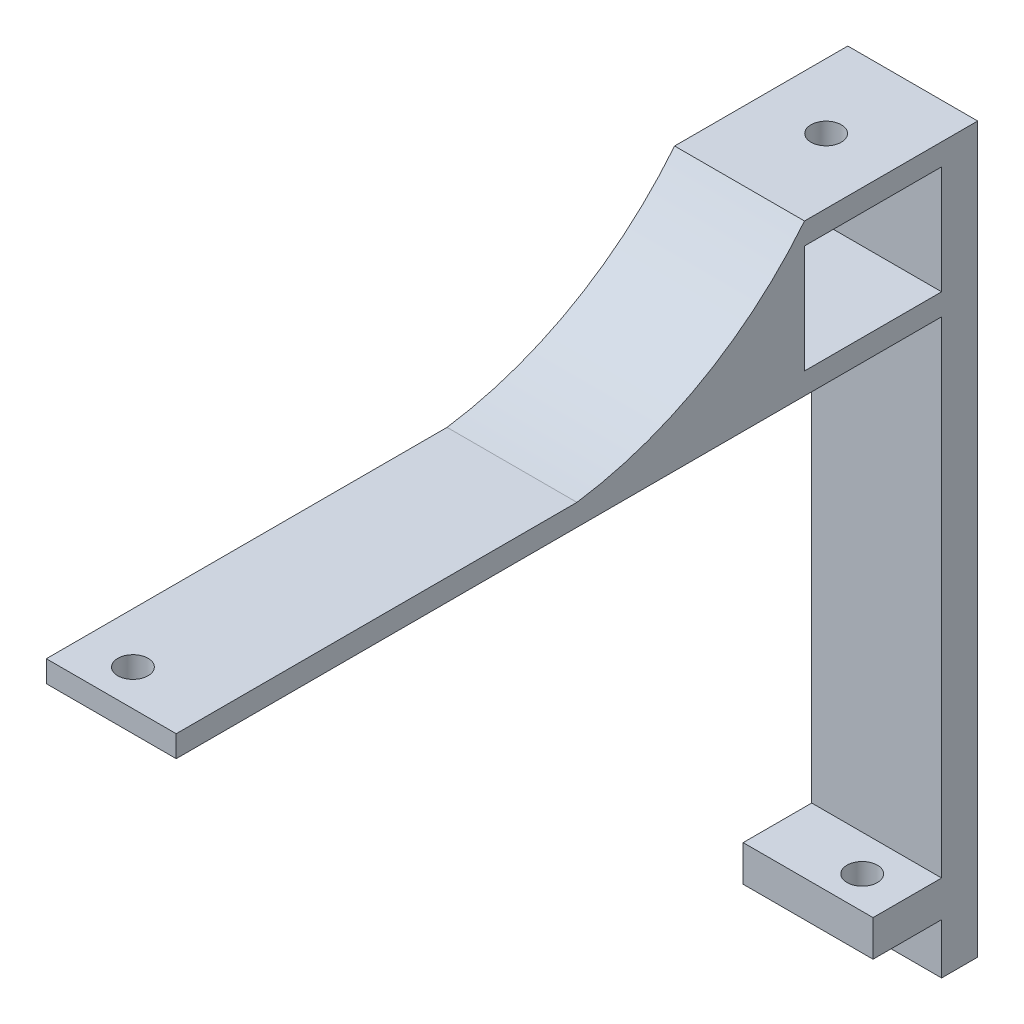
SolidWorks part; units mm, degrees
ref_plane "Front Plane" through (0, 0, 0) normal (0, 0, 1) x (1, 0, 0)
ref_plane "Top Plane" through (0, 0, 0) normal (0, 1, 0) x (1, 0, 0)
ref_plane "Right Plane" through (0, 0, 0) normal (1, 0, 0) x (0, 0, -1)
sketch "Sketch3" plane through (0, 0, 0) normal (1, 0, 0) x (0, 0, -1)
  line L1 (22.6396, 117.064) -> (32.6396, 117.064)
  line L2 (22.6396, 117.064) -> (22.6396, 192.4144)
  line L3 (22.6396, 192.4144) -> (32.6396, 192.4144)
  line L4 (32.6396, 117.064) -> (32.6396, 192.4144)
  line L6 (-73.4248, 192.4144) -> (22.6396, 192.4144)
  line L8 (-73.4248, 189.4144) -> (22.6396, 189.4144)
  line L9 (22.6396, 192.4144) -> (22.6396, 189.4144)
  line L10 (-63.4248, 192.4144) -> (-63.4248, 189.4144)
  line L11 (-73.4248, 192.4144) -> (-73.4248, 189.4144)
  line L12 (37.6396, 117.064) -> (32.6396, 117.064)
  line L13 (32.6396, 192.4144) -> (37.6396, 192.4144)
  line L14 (32.6396, 192.4144) -> (32.6396, 110.064)
  line L15 (32.6396, 110.064) -> (37.6396, 110.064)
  line L16 (37.6396, 192.4144) -> (37.6396, 110.064)
  line L17 (32.6396, 122.064) -> (22.6396, 122.064)
  dimension "D1" = 10
  dimension "D2" = 0
  dimension "D3" = 10
  dimension "D4" = 5
  dimension "D5" = 5
sketch "Sketch4" plane through (0, 0, 0) normal (1, 0, 0) x (0, 0, -1)
  line L1 (22.6396, 122.064) -> (32.6396, 122.064)
  line L2 (22.6396, 122.064) -> (22.6396, 117.064)
  line L3 (22.6396, 117.064) -> (32.6396, 117.064)
  line L4 (32.6396, 122.064) -> (32.6396, 117.064)
  line L5 (37.6396, 110.064) -> (32.6396, 110.064)
  line L6 (37.6396, 110.064) -> (37.6396, 192.4144)
  line L7 (37.6396, 192.4144) -> (32.6396, 192.4144)
  line L8 (32.6396, 110.064) -> (32.6396, 192.4144)
  line L9 (-73.4248, 192.4144) -> (32.6396, 192.4144)
  line L10 (-73.4248, 192.4144) -> (-73.4248, 189.4144)
  line L11 (-73.4248, 189.4144) -> (32.6396, 189.4144)
  line L12 (32.6396, 192.4144) -> (32.6396, 189.4144)
extrude "Boss-Extrude1" add sketch "Sketch4" along normal blind 52 contours L10 L11 L8 L9 | L8 L5 L6 L7 L4 | L4 L1 L2 L3
sketch "Sketch5" plane through (0, 122.064, 0) normal (0, 1, 0) x (1, 0, 0)
  line L0 (26, 22.6396) -> (26, 32.6396) construction
  line L1 (52, 22.6396) -> (0, 22.6396) construction
  line L2 (52, 32.6396) -> (0, 32.6396) construction
  circle A0 centre (6, 27.0496) radius 2.1
  circle A1 centre (46, 27.6396) radius 2.1
  dimension "D1" = 4.2
  dimension "D2" = 4.2
  dimension "D3" = 20
  dimension "D4" = 20
  dimension "D5" = 4.41
  dimension "D6" = 5
extrude "Cut-Extrude1" cut sketch "Sketch5" against normal blind 52
sketch "Sketch6" plane through (0, 192.4144, 0) normal (0, 1, 0) x (1, 0, 0)
  line L0 (52, -73.4248) -> (0, -73.4248) construction
  line L1 (26, -73.4248) -> (26, -63.8952) construction
  circle A0 centre (41, -68.4248) radius 2.1
  circle A1 centre (11, -68.4248) radius 2.1
  dimension "D1" = 4.2
  dimension "D2" = 5
  dimension "D3" = 15
extrude "Cut-Extrude2" cut sketch "Sketch6" against normal blind 52
sketch "Sketch7" plane through (0, 0, -37.6396) normal (0, 0, -1) x (-1, 0, 0)
  line L0 (-26, 192.4144) -> (-26, 110.064) construction
  line L1 (-52, 192.4144) -> (0, 192.4144) construction
  line L2 (-52, 110.064) -> (0, 110.064) construction
  line L3 (-18, 192.4144) -> (-18, 110.064)
  line L4 (-18, 192.4144) -> (-34, 192.4144)
  line L5 (-26, 192.4144) -> (-26, 110.064)
  line L6 (-18, 110.064) -> (-34, 110.064)
  line L7 (-34, 192.4144) -> (-34, 110.064)
  line M9 (-52, 110.064) -> (0, 110.064)
  dimension "D1" = 8
extrude "Cut-Extrude4" cut sketch "Sketch7" against normal blind 124 contours L4 L7 L5 M9
sketch "Sketch8" plane through (0, 0, 0) normal (-1, 0, 0) x (0, 0, 1)
  line L0 (-37.6396, 192.4144) -> (-37.6396, 210.4144)
  line L1 (-37.6396, 210.4144) -> (-13.6396, 210.4144)
  line L2 (73.4248, 192.4144) -> (-37.6396, 192.4144) construction
  line L3 (-37.6396, 192.4144) -> (17.8926, 192.4144)
  line L4 (-32.6396, 192.4144) -> (-32.6396, 207.4144)
  line L5 (-32.6396, 207.4144) -> (-13.6396, 207.4144)
  line L6 (-13.6396, 207.4144) -> (-13.6396, 192.4144)
  arc A0 (-13.6396, 210.4144) -> (17.8926, 192.4144) centre (25.0593, 241.5878) ccw
  line M8 (73.4248, 192.4144) -> (-37.6396, 192.4144)
  dimension "D1" = 18
  dimension "D2" = 24
  dimension "D3" = 5
  dimension "D4" = 3
extrude "Boss-Extrude2" add sketch "Sketch8" against normal up to surface (18 mm away) contours A0 L1 L0 L3 L4 L5 L6 M8 up to face at (18, 146.2041, -10.4267)
sketch "Sketch9" plane through (0, 210.4144, 0) normal (0, 1, 0) x (1, 0, 0)
  line L0 (9, 13.6396) -> (9, 37.6396) construction
  line L1 (18, 13.6396) -> (0, 13.6396) construction
  line L2 (18, 37.6396) -> (0, 37.6396) construction
  line L3 (0, 25.6396) -> (18, 25.6396) construction
  line L4 (0, 37.6396) -> (0, 13.6396) construction
  line L5 (18, 37.6396) -> (18, 13.6396) construction
  circle A0 centre (9, 25.6396) radius 2.1
  dimension "D1" = 4.2
extrude "Cut-Extrude5" cut sketch "Sketch9" against normal blind 6
sketch "Sketch11" plane through (52, 0, 0) normal (1, 0, 0) x (0, 0, -1)
  line L0 (32.6396, 192.4144) -> (37.6396, 192.4144)
  line L1 (37.6396, 192.4144) -> (37.6396, 210.4144)
  line L2 (37.6396, 210.4144) -> (13.6396, 210.4144)
  line L3 (32.6396, 192.4144) -> (32.6396, 207.4144)
  line L4 (32.6396, 207.4144) -> (13.6396, 207.4144)
  line L5 (13.6396, 207.4144) -> (13.6396, 192.4144)
  line L6 (13.6396, 192.4144) -> (-17.8926, 192.4144)
  line L7 (-73.4248, 192.4144) -> (37.6396, 192.4144) construction
  arc A0 (13.6396, 210.4144) -> (-17.8926, 192.4144) centre (-25.0593, 241.5878) cw
extrude "Boss-Extrude3" add sketch "Sketch11" against normal up to surface (18 mm away) up to face at (34, 146.2041, -10.4267)
sketch "Sketch12" plane through (0, 210.4144, 0) normal (0, 1, 0) x (1, 0, 0)
  line L0 (43, 37.6396) -> (43, 13.6396) construction
  line L1 (34, 37.6396) -> (52, 37.6396) construction
  line L2 (34, 13.6396) -> (52, 13.6396) construction
  line L3 (34, 25.6396) -> (52, 25.6396) construction
  line L4 (34, 13.6396) -> (34, 37.6396) construction
  line L5 (52, 37.6396) -> (52, 13.6396) construction
  circle A0 centre (43, 25.6396) radius 2.1
  dimension "D1" = 4.2
extrude "Cut-Extrude7" cut sketch "Sketch12" against normal blind 11
sketch "Sketch13" plane through (0, 210.4144, 0) normal (0, 1, 0) x (1, 0, 0)
  line L1 (-6.2363, 41.7302) -> (24.5227, 41.7302)
  line L2 (-6.2363, 41.7302) -> (-6.2363, -77.0804)
  line L3 (-6.2363, -77.0804) -> (24.5227, -77.0804)
  line L4 (24.5227, 41.7302) -> (24.5227, -77.0804)
extrude "Cut-Extrude8" cut sketch "Sketch13" against normal blind 134
sketch "Sketch14" plane through (0, 122.064, 0) normal (0, 1, 0) x (1, 0, 0)
  line L0 (34, 22.6396) -> (34, 32.6396) construction
  line L1 (34, 24.6396) -> (52, 24.6396)
  line L2 (34, 24.6396) -> (34, 22.6396)
  line L3 (34, 22.6396) -> (52, 22.6396)
  line L4 (52, 24.6396) -> (52, 22.6396)
  dimension "D1" = 2
extrude "Cut-Extrude9" cut sketch "Sketch14" against normal blind 10
sketch "Sketch15" plane through (0, 122.064, 0) normal (0, 1, 0) x (1, 0, 0)
  line L1 (34, 32.6396) -> (52, 32.6396)
  line L2 (34, 32.6396) -> (34, 22.6396)
  line L3 (34, 22.6396) -> (52, 22.6396)
  line L4 (52, 32.6396) -> (52, 22.6396)
  dimension "D1" = 10
extrude "Boss-Extrude4" add sketch "Sketch15" against normal up to vertex
sketch "Sketch16" plane through (0, 122.064, 0) normal (0, 1, 0) x (1, 0, 0)
  line L0 (52, 27.6396) -> (26, 27.6396) construction
  line L1 (52, 22.6396) -> (52, 32.6396) construction
  circle A0 centre (46, 27.6396) radius 2.1
  dimension "D2" = 4.2
  dimension "D3" = 20
  dimension "D1" = 26
extrude "Cut-Extrude10" cut sketch "Sketch16" against normal blind 68
sketch "Sketch17" plane through (0, 192.4144, 0) normal (0, 1, 0) x (1, 0, 0)
  circle A0 centre (41, -68.4248) radius 2.1
extrude "Boss-Extrude5" add sketch "Sketch17" against normal up to surface (3 mm away) up to face at (41, 189.4144, 70.5248)
sketch "Sketch18" plane through (0, 192.4144, 0) normal (0, 1, 0) x (1, 0, 0)
  line L0 (52, -67.8904) -> (26, -67.8904) construction
  line L1 (52, -73.4248) -> (52, -17.8926) construction
  line L2 (52, -73.4248) -> (34, -73.4248) construction
  circle A0 centre (41, -68.4248) radius 2.1
  dimension "D2" = 4.2
  dimension "D3" = 15
  dimension "D4" = 5
  dimension "D1" = 26
extrude "Cut-Extrude11" cut sketch "Sketch18" against normal blind 68 contours A0
sketch "Sketch19" plane through (0, 122.064, 0) normal (0, 1, 0) x (1, 0, 0)
  line L0 (52, 22.6396) -> (52, 32.6396) construction
  line L1 (34, 22.6396) -> (52, 22.6396)
  line L2 (34, 22.6396) -> (34, 23.1396)
  line L3 (34, 23.1396) -> (52, 23.1396)
  line L4 (52, 22.6396) -> (52, 23.1396)
  dimension "D1" = 0.5
extrude "Cut-Extrude12" cut sketch "Sketch19" against normal blind 68
sketch "Sketch20" plane through (0, 122.064, 0) normal (0, 1, 0) x (1, 0, 0)
  line L1 (41.9876, 32.8659) -> (49.875, 32.8659)
  line L2 (41.9876, 32.8659) -> (41.9876, 24.8659)
  line L3 (41.9876, 24.8659) -> (49.875, 24.8659)
  line L4 (49.875, 32.8659) -> (49.875, 24.8659)
  dimension "D1" = 8
extrude "Boss-Extrude6" add sketch "Sketch20" against normal up to surface (5 mm away) up to face at (46, 117.064, -25.5396)
sketch "Sketch21" plane through (0, 122.064, 0) normal (0, 1, 0) x (1, 0, 0)
  line L0 (52, 32.6396) -> (34, 32.6396) construction
  line L1 (52, 27.8896) -> (26, 27.8896) construction
  line L2 (52, 23.1396) -> (52, 32.6396) construction
  circle A0 centre (46, 27.6396) radius 2.1
  dimension "D1" = 5
  dimension "D2" = 4.2
  dimension "D4" = 20
  dimension "D3" = 26
extrude "Cut-Extrude13" cut sketch "Sketch21" against normal blind 10 contours A0
